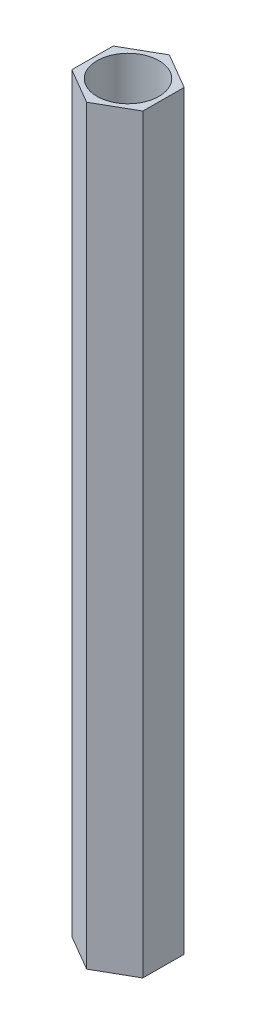
SolidWorks part; units mm, degrees
ref_plane "Front Plane" through (0, 0, 0) normal (0, 0, 1) x (1, 0, 0)
ref_plane "Top Plane" through (0, 0, 0) normal (0, 1, 0) x (1, 0, 0)
ref_plane "Right Plane" through (0, 0, 0) normal (1, 0, 0) x (0, 0, -1)
sketch "Sketch1" plane through (0, 0, 0) normal (0, 1, 0) x (1, 0, 0)
  line L1 (1.8945, -1.1065) -> (1.9055, 1.0874)
  line L2 (1.9055, 1.0874) -> (0.011, 2.1939)
  line L3 (0.011, 2.1939) -> (-1.8945, 1.1065)
  line L4 (-1.8945, 1.1065) -> (-1.9055, -1.0874)
  line L5 (-1.9055, -1.0874) -> (-0.011, -2.1939)
  line L6 (-0.011, -2.1939) -> (1.8945, -1.1065)
  circle A0 centre (0, 0) radius 1.9 construction
  circle A1 centre (0, 0) radius 1.65
  dimension "D1" = 3.3
  dimension "D2" = 3.8
extrude "Boss-Extrude1" add sketch "Sketch1" along normal blind 40
